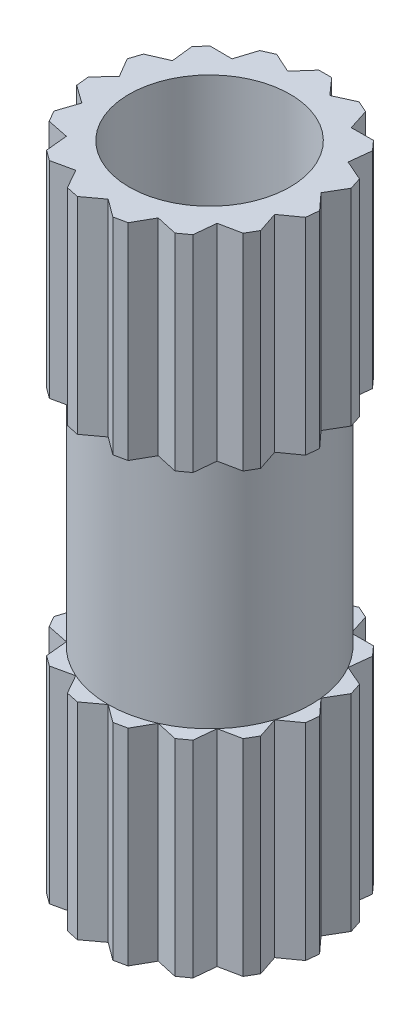
SolidWorks part; units mm, degrees
ref_plane "Front Plane" through (0, 0, 0) normal (0, 0, 1) x (1, 0, 0)
ref_plane "Top Plane" through (0, 0, 0) normal (0, 1, 0) x (1, 0, 0)
ref_plane "Right Plane" through (0, 0, 0) normal (1, 0, 0) x (0, 0, -1)
sketch "Sketch1" plane through (0, 0, 0) normal (0, 1, 0) x (1, 0, 0)
  circle A0 centre (0, 0) radius 1.575
  circle A1 centre (0, 0) radius 1.25
  dimension "D1" = 3.15
  dimension "D2" = 2.5
extrude "Boss-Extrude1" add sketch "Sketch1" along normal blind 5
sketch "Sketch2" plane through (0, 5, 0) normal (0, 1, 0) x (1, 0, 0)
  line L0 (0, 0) -> (0, 1.8) construction
  line L1 (0, 0) -> (-0.3742, 1.7607) construction
  line L2 (-0.3275, 1.5406) -> (-0.1, 1.7972)
  line L3 (-0.1, 1.7972) -> (0.1, 1.7972)
  line L4 (0.3275, 1.5406) -> (0.6396, 1.6825)
  line L5 (0.3275, 1.5406) -> (0.1, 1.7972)
  line L6 (0.6396, 1.6825) -> (0.8223, 1.6012)
  line L7 (0.9258, 1.2742) -> (0.8223, 1.6012)
  line L8 (0.9258, 1.2742) -> (1.2687, 1.2769)
  line L9 (1.2687, 1.2769) -> (1.4025, 1.1283)
  line L10 (1.364, 0.7875) -> (1.4025, 1.1283)
  line L11 (1.364, 0.7875) -> (1.6784, 0.6505)
  line L12 (1.6784, 0.6505) -> (1.7402, 0.4603)
  line L13 (1.5664, 0.1646) -> (1.7402, 0.4603)
  line L14 (1.5664, 0.1646) -> (1.7978, -0.0884)
  line L15 (1.7978, -0.0884) -> (1.7769, -0.2873)
  line L16 (1.4979, -0.4867) -> (1.7769, -0.2873)
  line L17 (1.4979, -0.4867) -> (1.6064, -0.812)
  line L18 (1.6064, -0.812) -> (1.5064, -0.9852)
  line L19 (1.1705, -1.0539) -> (1.5064, -0.9852)
  line L20 (1.1705, -1.0539) -> (1.1373, -1.3952)
  line L21 (1.1373, -1.3952) -> (0.9755, -1.5128)
  line L22 (0.6406, -1.4388) -> (0.9755, -1.5128)
  line L23 (0.6406, -1.4388) -> (0.4715, -1.7372)
  line L24 (0.4715, -1.7372) -> (0.2758, -1.7787)
  line L25 (0, -1.575) -> (0.2758, -1.7787)
  line L26 (0, -1.575) -> (-0.2758, -1.7787)
  line L27 (-0.2758, -1.7787) -> (-0.4715, -1.7372)
  line L28 (-0.6406, -1.4388) -> (-0.4715, -1.7372)
  line L29 (-0.6406, -1.4388) -> (-0.9755, -1.5128)
  line L30 (-0.9755, -1.5128) -> (-1.1373, -1.3952)
  line L31 (-1.1705, -1.0539) -> (-1.1373, -1.3952)
  line L32 (-1.1705, -1.0539) -> (-1.5064, -0.9852)
  line L33 (-1.5064, -0.9852) -> (-1.6064, -0.812)
  line L34 (-1.4979, -0.4867) -> (-1.6064, -0.812)
  line L35 (-1.4979, -0.4867) -> (-1.7769, -0.2873)
  line L36 (-1.7769, -0.2873) -> (-1.7978, -0.0884)
  line L37 (-1.5664, 0.1646) -> (-1.7978, -0.0884)
  line L38 (-1.5664, 0.1646) -> (-1.7402, 0.4603)
  line L39 (-1.7402, 0.4603) -> (-1.6784, 0.6505)
  line L40 (-1.364, 0.7875) -> (-1.6784, 0.6505)
  line L41 (-1.364, 0.7875) -> (-1.4025, 1.1283)
  line L42 (-1.4025, 1.1283) -> (-1.2687, 1.2769)
  line L43 (-0.9258, 1.2742) -> (-1.2687, 1.2769)
  line L44 (-0.9258, 1.2742) -> (-0.8223, 1.6012)
  line L45 (-0.8223, 1.6012) -> (-0.6396, 1.6825)
  line L46 (-0.3275, 1.5406) -> (-0.6396, 1.6825)
  circle A0 centre (0, 0) radius 1.575 construction
  circle A22 centre (0, 0) radius 1.25 construction
  circle A23 centre (0, 0) radius 1.25
  circle A24 centre (0, 0) radius 1.8
  circle A25 centre (0, 0) radius 1.575
  point P69 (0, 0)
  dimension "D1" = 3.6
  dimension "D3" = 12
  dimension "D4" = 0.2
extrude "Boss-Extrude2" add sketch "Sketch2" against normal blind 3.2
mirror "Mirror1" about plane through (0, 0, 0) normal (0, 1, 0) of "Boss-Extrude1", "Boss-Extrude2"
